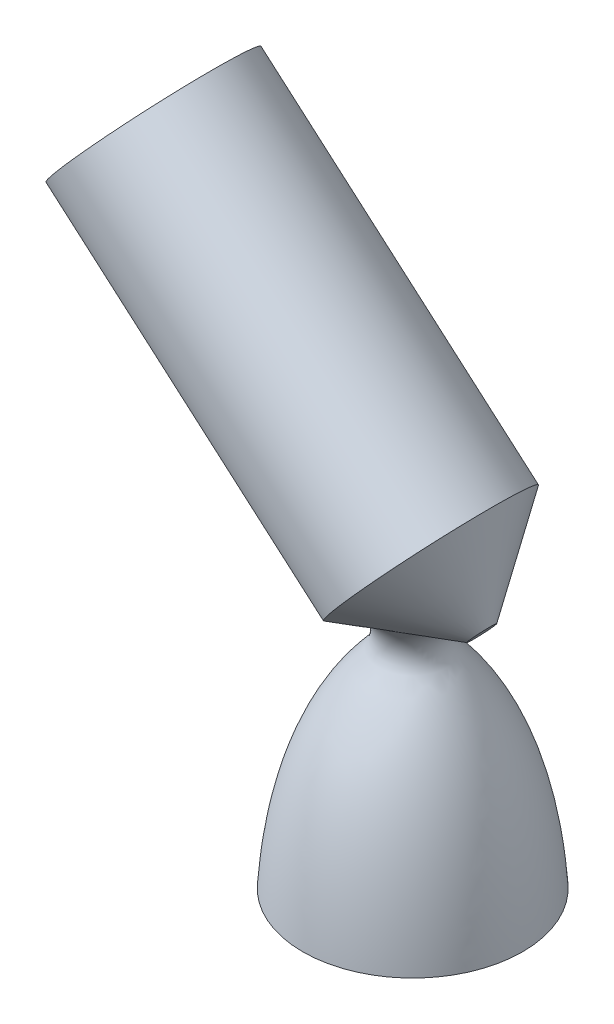
SolidWorks part; units mm, degrees
ref_plane "Front Plane" through (0, 0, 0) normal (0, 0, 1) x (1, 0, 0)
ref_plane "Top Plane" through (0, 0, 0) normal (0, 1, 0) x (1, 0, 0)
ref_plane "Right Plane" through (0, 0, 0) normal (1, 0, 0) x (0, 0, -1)
sketch "Sketch1" plane through (0, 0, 0) normal (0, 0, 1) x (1, 0, 0)
  line L0 (1015.2504, -199.8859) -> (1015.2504, -290.3347) construction
  line L1 (1034.9636, -271.3945) -> (1038.8289, -271.3945)
  line L2 (1030.5006, -206.266) -> (1015.2504, -206.266)
  line L3 (1015.2504, -206.266) -> (1015.2504, -232.7412)
  line L4 (1015.2504, -232.7412) -> (1034.9636, -271.3945)
  spline S0 degree 3 poles (1038.8289, -271.3945) (1037.8734, -256.437) (1033.9324, -239.0283) (1022.0455, -226.1973) (1021.3856, -223.2499) (1023.4616, -215.8804) (1031.8025, -213.51) (1030.5006, -206.266) knots 0 0 0 0 0.648974 0.689713 0.725949 0.770742 1 1 1 1
sketch "Sketch2" plane through (0, 0, 0) normal (0, 0, 1) x (1, 0, 0)
  line L0 (1030.0613, -216.5844) -> (959.6572, -155.3954)
  line L1 (959.6572, -155.3954) -> (972.3149, -140.8315)
  line L2 (1030.0613, -216.5844) -> (1031.821, -214.5597)
  line L3 (972.3149, -140.8315) -> (1031.821, -192.5489)
  line L4 (964.2454, -159.3831) -> (1031.821, -196.0993) construction
  line L5 (964.2454, -159.3831) -> (972.3149, -140.8315) construction
  line L6 (1030.0613, -216.5844) -> (959.6572, -155.3954) construction
  line L7 (1031.821, -192.5489) -> (1031.821, -214.5597)
  point P1 (964.2454, -159.3831)
revolve "Revolve1" add sketch "Sketch2" angle 360 about L0
revolve "Revolve2" add sketch "Sketch1" angle 360 about L0
